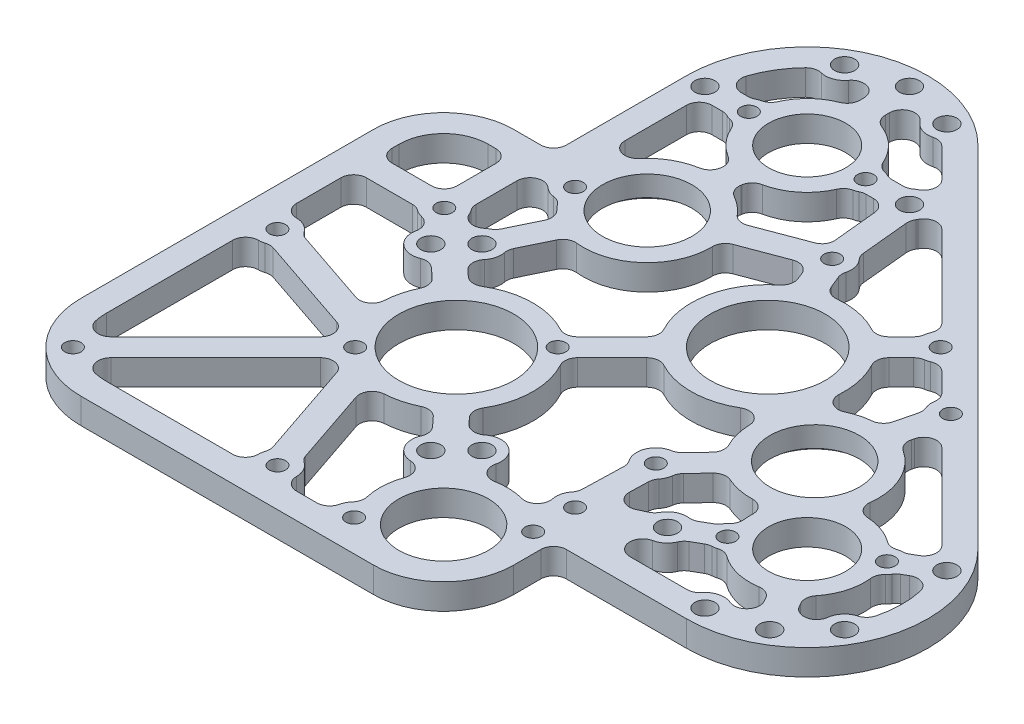
SolidWorks part; units mm, degrees
ref_plane "Front Plane" through (0, 0, 0) normal (0, 0, 1) x (1, 0, 0)
ref_plane "Top Plane" through (0, 0, 0) normal (0, 1, 0) x (1, 0, 0)
ref_plane "Right Plane" through (0, 0, 0) normal (1, 0, 0) x (0, 0, -1)
ref_plane "Plane1" through (0, 3.175, 0) normal (0, 1, 0) x (1, 0, 0)
sketch "Sketch1" plane through (0, 3.175, 0) normal (0, 1, 0) x (1, 0, 0)
  line L0 (-29.84, 86.9695) -> (-29.84, -29.84)
  line L1 (-29.84, -29.84) -> (86.9695, -29.84)
  line L2 (108.1827, 21.3732) -> (21.3732, 108.1827)
  arc A0 (86.9695, -29.84) -> (108.1827, 21.3732) centre (86.9695, 0.16) ccw
  arc A1 (21.3732, 108.1827) -> (-29.84, 86.9695) centre (0.16, 86.9695) ccw
extrude "Boss-Extrude1" add sketch "Sketch1" against normal blind 6.35
sketch "Sketch2" plane through (0, 0, 29.84) normal (0, 0, 1) x (1, 0, 0)
  line L0 (-29.84, 3.175) -> (53.975, 3.175)
  line L1 (53.975, 3.175) -> (53.975, -3.175)
  line L2 (53.975, -3.175) -> (-29.84, -3.175)
  line L3 (-29.84, -3.175) -> (-29.84, 3.175)
extrude "Boss-Extrude2" add sketch "Sketch2" along normal blind 27.31
sketch "Sketch3" plane through (-29.84, 0, 0) normal (-1, 0, 0) x (0, 0, 1)
  line L0 (-53.975, 3.175) -> (57.15, 3.175)
  line L1 (57.15, 3.175) -> (57.15, -3.175)
  line L2 (57.15, -3.175) -> (-53.975, -3.175)
  line L3 (-53.975, -3.175) -> (-53.975, 3.175)
extrude "Boss-Extrude3" add sketch "Sketch3" along normal blind 27.31
sketch "Sketch4" plane through (0, 3.175, 0) normal (0, 1, 0) x (-1, 0, 0)
  line L0 (-29.0653, -83.7455) -> (-30.4558, -69.5226)
  line L1 (-31.9225, -63.5944) -> (-34.5089, -57.2592)
  line L2 (-49.7059, -54.196) -> (-55.383, -59.8731)
  line L3 (-56.9235, -63.6521) -> (-34.9066, -85.6689)
  arc A0 (-34.9066, -85.6689) -> (-29.8209, -84.8421) centre (-32.6616, -83.4239) ccw
  arc A1 (-29.8209, -84.8421) -> (-29.0653, -83.7455) centre (-25.56, -86.9695) cw
  arc A2 (-30.4558, -69.5226) -> (-31.9225, -63.5944) centre (-27.6413, -65.6808) cw
  arc A3 (-34.5089, -57.2592) -> (-49.7059, -54.196) centre (-38.669, -38.669) cw
  arc A4 (-55.383, -59.8731) -> (-56.9235, -63.6521) centre (-60.1381, -60.1381) cw
extrude "Cut-Extrude1" cut sketch "Sketch4" against normal through all
sketch "Sketch5" plane through (0, 3.175, 0) normal (0, 1, 0) x (-1, 0, 0)
  line L0 (-96.6842, 10.3165) -> (-98.3364, 13.1781)
  line L1 (-105.4145, -7.1431) -> (-103.2213, -5.8768)
  arc A0 (-98.3364, 13.1781) -> (-104.2382, 11.9704) centre (-101.086, 11.5906) ccw
  arc A1 (-104.2382, 11.9704) -> (-109.2448, 7.7857) centre (-108.9665, 12.54) cw
  arc A2 (-109.2448, 7.7857) -> (-110.1084, -5.0499) centre (-86.9695, -0.16) ccw
  arc A3 (-110.1084, -5.0499) -> (-105.4145, -7.1431) centre (-107.002, -4.3934) ccw
  arc A4 (-103.2213, -5.8768) -> (-100.8296, -3.6281) centre (-99.5268, -7.41) cw
  arc A5 (-100.8296, -3.6281) -> (-96.6842, 10.3165) centre (-86.9695, -0.16) cw
extrude "Cut-Extrude2" cut sketch "Sketch5" against normal through all
sketch "Sketch6" plane through (0, 3.175, 0) normal (0, 1, 0) x (-1, 0, 0)
  line L0 (16.0612, -10.244) -> (22.0527, -15.6622)
  line L1 (35.0088, -25.2744) -> (50.8, -25.2744)
  line L2 (50.8, -25.2744) -> (50.8, -6.7248)
  line L3 (43.2449, -5.0448) -> (23.2061, 1.7351)
  arc A0 (23.2061, 1.7351) -> (19.0188, -1.0906) centre (22.1885, -1.2724) ccw
  arc A1 (19.0188, -1.0906) -> (16.0612, -10.244) centre (0, 0) cw
  arc A2 (22.0527, -15.6622) -> (30.0588, -20.0384) centre (25.4, -19.05) cw
  arc A3 (30.0588, -20.0384) -> (32.4824, -23.7981) centre (33.1647, -20.6973) ccw
  arc A4 (32.4824, -23.7981) -> (35.0088, -25.2744) centre (31.459, -28.4494) cw
  arc A5 (50.8, -6.7248) -> (43.2449, -5.0448) centre (47.625, -3.175) cw
extrude "Cut-Extrude3" cut sketch "Sketch6" against normal through all
sketch "Sketch7" plane through (0, 3.175, 0) normal (0, 1, 0) x (-1, 0, 0)
  line L0 (-24.2595, -96.3161) -> (-15.5435, -105.032)
  line L1 (-3.335, -104.204) -> (-3.335, -100.8997)
  line L2 (-17.093, -90.1445) -> (-22.0102, -90.1445)
  arc A0 (-22.0102, -90.1445) -> (-23.4326, -91.2304) centre (-25.56, -86.9695) cw
  arc A1 (-23.4326, -91.2304) -> (-24.2595, -96.3161) centre (-22.0144, -94.0711) ccw
  arc A2 (-15.5435, -105.032) -> (-9.05, -106.109) centre (-12.86, -108.9665) cw
  arc A3 (-9.05, -106.109) -> (-3.335, -104.204) centre (-6.51, -104.204) ccw
  arc A4 (-3.335, -100.8997) -> (-13.8973, -90.8961) centre (-0.16, -86.9695) cw
  arc A5 (-13.8973, -90.8961) -> (-17.093, -90.1445) centre (-14.66, -86.9695) cw
extrude "Cut-Extrude4" cut sketch "Sketch7" against normal through all
sketch "Sketch8" plane through (0, 3.175, 0) normal (0, 1, 0) x (-1, 0, 0)
  line L0 (-28.6299, -54.8591) -> (-25.8697, -61.6201)
  line L1 (-25.8697, -61.6201) -> (-9.958, -55.6236)
  line L2 (9.5999, -37.7167) -> (14.6498, -27.222)
  line L3 (18.1765, -20.7183) -> (11.8021, -14.9537)
  line L4 (-11.0369, -15.527) -> (-23.1419, -27.6321)
  arc A0 (-23.1419, -27.6321) -> (-28.6299, -54.8591) centre (-38.669, -38.669) cw
  arc A1 (-9.958, -55.6236) -> (9.5999, -37.7167) centre (5.7166, -53.1094) cw
  arc A2 (14.6498, -27.222) -> (18.1765, -20.7183) centre (19.05, -25.4) cw
  arc A3 (11.8021, -14.9537) -> (-11.0369, -15.527) centre (0, 0) cw
extrude "Cut-Extrude5" cut sketch "Sketch8" against normal through all
sketch "Sketch9" plane through (0, 3.175, 0) normal (0, 1, 0) x (-1, 0, 0)
  line L0 (-66.5703, 23.49) -> (-82.5401, 23.49)
  line L1 (-92.8371, 16.3531) -> (-91.185, 13.4915)
  line L2 (-73.8926, 11.0561) -> (-69.6341, 13.5148)
  arc A0 (-69.6341, 13.5148) -> (-65.9311, 17.205) centre (-64.9724, 12.54) cw
  arc A1 (-65.9311, 17.205) -> (-66.5703, 23.49) centre (-66.5703, 20.315) ccw
  arc A2 (-82.5401, 23.49) -> (-88.8403, 20.8604) centre (-86.9695, 25.24) cw
  arc A3 (-88.8403, 20.8604) -> (-92.8371, 16.3531) centre (-90.0875, 17.9406) ccw
  arc A4 (-91.185, 13.4915) -> (-77.0359, 10.1092) centre (-86.9695, -0.16) cw
  arc A5 (-77.0359, 10.1092) -> (-73.8926, 11.0561) centre (-74.4121, 7.09) cw
extrude "Cut-Extrude6" cut sketch "Sketch9" against normal through all
sketch "Sketch10" plane through (0, 3.175, 0) normal (0, 1, 0) x (-1, 0, 0)
  line L0 (-60.5829, -6.5299) -> (-54.5042, -0.1488)
  line L1 (-52.8316, 3.8684) -> (-52.6706, 9.6387)
  line L2 (-57.1631, 12.6155) -> (-60.4246, 11.1263)
  line L3 (-66.4591, 8.0155) -> (-70.7176, 5.5569)
  arc A0 (-73.4343, -4.7351) -> (-60.5829, -6.5299) centre (-69.0125, -19.9819) cw
  arc A1 (-54.5042, -0.1488) -> (-52.8316, 3.8684) centre (-49.7569, 0.2314) cw
  arc A2 (-52.6706, 9.6387) -> (-57.1631, 12.6155) centre (-55.8443, 9.7273) ccw
  arc A3 (-60.4246, 11.1263) -> (-66.4591, 8.0155) centre (-64.9724, 12.54) cw
  arc A4 (-70.7176, 5.5569) -> (-73.1093, 3.3081) centre (-74.4121, 7.09) cw
  arc A5 (-73.1093, 3.3081) -> (-73.4343, -4.7351) centre (-86.9695, -0.16) cw
extrude "Cut-Extrude7" cut sketch "Sketch10" against normal through all
sketch "Sketch11" plane through (0, 3.175, 0) normal (0, 1, 0) x (-1, 0, 0)
  line L0 (36.1273, 50.8) -> (0.3748, 50.8)
  line L1 (0.9702, 45.2801) -> (9.3987, 20.3689)
  line L2 (14.6513, 19.1414) -> (40.6599, 45.1501)
  arc A0 (0.3748, 50.8) -> (0.9702, 45.2801) centre (-3.175, 47.625) cw
  arc A1 (9.3987, 20.3689) -> (14.6513, 19.1414) centre (12.4062, 21.3865) ccw
  arc A2 (40.6599, 45.1501) -> (39.0466, 50.5067) centre (38.4149, 47.3951) ccw
  arc A3 (39.0466, 50.5067) -> (36.1273, 50.8) centre (36.1273, 36.1273) ccw
extrude "Cut-Extrude8" cut sketch "Sketch11" against normal through all
sketch "Sketch12" plane through (0, 3.175, 0) normal (0, 1, 0) x (-1, 0, 0)
  line L0 (28.284, -43.3699) -> (28.284, -31.9991)
  line L1 (20.3718, -29.9754) -> (15.3219, -40.4701)
  arc A0 (28.284, -31.9991) -> (27.0619, -30.2789) centre (31.459, -28.4494) cw
  arc A1 (27.0619, -30.2789) -> (22.0983, -29.0591) centre (24.1305, -31.4985) ccw
  arc A2 (22.0983, -29.0591) -> (20.3718, -29.9754) centre (19.05, -25.4) cw
  arc A3 (15.3219, -40.4701) -> (19.0537, -44.4991) centre (5.7166, -53.1094) cw
  arc A4 (19.0537, -44.4991) -> (22.9599, -45.7069) centre (19.7361, -49.2125) cw
  arc A5 (22.9599, -45.7069) -> (28.284, -43.3699) centre (25.109, -43.3699) ccw
extrude "Cut-Extrude9" cut sketch "Sketch12" against normal through all
sketch "Sketch13" plane through (0, 3.175, 0) normal (0, 1, 0) x (-1, 0, 0)
  line L0 (-69.6829, -35.8427) -> (-71.8085, -44.3955)
  line L1 (-71.4484, -49.1272) -> (-63.6521, -56.9235)
  line L2 (-59.8731, -55.383) -> (-54.196, -49.7059)
  arc A0 (-54.196, -49.7059) -> (-57.6769, -37.4031) centre (-38.669, -38.669) cw
  arc A1 (-57.6769, -37.4031) -> (-62.2061, -34.3237) centre (-60.8449, -37.1921) ccw
  arc A2 (-62.2061, -34.3237) -> (-69.6829, -35.8427) centre (-69.0125, -19.9819) cw
  arc A3 (-71.8085, -44.3955) -> (-71.4484, -49.1272) centre (-75.7459, -47.0747) cw
  arc A4 (-63.6521, -56.9235) -> (-59.8731, -55.383) centre (-60.1381, -60.1381) cw
extrude "Cut-Extrude10" cut sketch "Sketch13" against normal through all
sketch "Sketch14" plane through (0, 3.175, 0) normal (0, 1, 0) x (-1, 0, 0)
  line L0 (-46.1378, 16.0992) -> (-46.4841, 3.6912)
  line L1 (-49.9065, -4.5287) -> (-55.9852, -10.9098)
  line L2 (-27.6321, -23.1419) -> (-15.527, -11.0369)
  line L3 (-15.0548, 11.6729) -> (-20.7797, 17.895)
  arc A0 (-44.546, 20.6875) -> (-46.1378, 16.0992) centre (-49.2125, 19.7361) cw
  arc A1 (-46.4841, 3.6912) -> (-49.9065, -4.5287) centre (-49.7569, 0.2314) cw
  arc A2 (-55.9852, -10.9098) -> (-53.142, -19.6057) centre (-69.0125, -19.9819) cw
  arc A3 (-53.142, -19.6057) -> (-48.3538, -22.2645) centre (-49.9679, -19.5304) ccw
  arc A4 (-48.3538, -22.2645) -> (-27.6321, -23.1419) centre (-38.669, -38.669) cw
  arc A5 (-15.527, -11.0369) -> (-15.0548, 11.6729) centre (0, 0) cw
  arc A6 (-20.7797, 17.895) -> (-30.0155, 20.2243) centre (-25.4, 19.05) cw
  arc A7 (-30.0155, 20.2243) -> (-33.6709, 24.129) centre (-33.0924, 21.0071) ccw
  arc A8 (-33.6709, 24.129) -> (-40.623, 24.3911) centre (-36.5633, 39.7383) cw
  arc A9 (-40.623, 24.3911) -> (-44.546, 20.6875) centre (-41.435, 21.3217) ccw
extrude "Cut-Extrude11" cut sketch "Sketch14" against normal through all
sketch "Sketch15" plane through (0, 3.175, 0) normal (0, 1, 0) x (-1, 0, 0)
  line L0 (-0.9062, -72.7015) -> (-0.0714, -67.8917)
  line L1 (-7.7187, -61.5657) -> (-22.0651, -66.9723)
  line L2 (-24.018, -70.1117) -> (-22.6803, -83.7945)
  line L3 (-22.6803, -83.7945) -> (-17.093, -83.7945)
  arc A0 (-0.0714, -67.8917) -> (-7.7187, -61.5657) centre (5.7166, -53.1094) cw
  arc A1 (-22.0651, -66.9723) -> (-23.5968, -68.1966) centre (-20.9454, -69.9433) ccw
  arc A2 (-23.5968, -68.1966) -> (-24.018, -70.1117) centre (-20.858, -69.8028) ccw
  arc A3 (-17.093, -83.7945) -> (-13.8973, -83.0428) centre (-14.66, -86.9695) cw
  arc A4 (-13.8973, -83.0428) -> (-0.9062, -72.7015) centre (-0.16, -86.9695) cw
extrude "Cut-Extrude12" cut sketch "Sketch15" against normal through all
sketch "Sketch16" plane through (0, 3.175, 0) normal (0, 1, 0) x (-1, 0, 0)
  line L0 (23.49, -83.7945) -> (23.49, -65.3482)
  line L1 (6.1851, -68.9775) -> (5.3503, -73.7873)
  line L2 (16.773, -83.7945) -> (23.49, -83.7945)
  arc A0 (23.49, -65.3482) -> (17.882, -63.3084) centre (20.315, -65.3482) ccw
  arc A1 (17.882, -63.3084) -> (6.1851, -68.9775) centre (5.7166, -53.1094) cw
  arc A2 (5.3503, -73.7873) -> (13.5774, -83.0428) centre (-0.16, -86.9695) cw
  arc A3 (13.5774, -83.0428) -> (16.773, -83.7945) centre (14.34, -86.9695) cw
extrude "Cut-Extrude13" cut sketch "Sketch16" against normal through all
sketch "Sketch17" plane through (0, 3.175, 0) normal (0, 1, 0) x (-1, 0, 0)
  line L0 (50.8, -31.6244) -> (34.634, -31.6244)
  line L1 (34.634, -31.6244) -> (34.634, -47.625)
  line L2 (34.634, -47.625) -> (50.8, -47.625)
  line L3 (50.8, -47.625) -> (50.8, -31.6244)
extrude "Cut-Extrude14" cut sketch "Sketch17" against normal through all
sketch "Sketch18" plane through (0, 3.175, 0) normal (0, 1, 0) x (-1, 0, 0)
  line L0 (-15.8286, 21.8923) -> (-10.3818, 15.9725)
  line L1 (1.7351, 23.2061) -> (-5.0448, 43.2449)
  line L2 (-6.7248, 50.8) -> (-19.3839, 50.8)
  arc A0 (-18.7949, 30.1557) -> (-15.8286, 21.8923) centre (-19.05, 25.4) cw
  arc A1 (-10.3818, 15.9725) -> (-1.0906, 19.0188) centre (0, 0) cw
  arc A2 (-1.0906, 19.0188) -> (1.7351, 23.2061) centre (-1.2724, 22.1885) ccw
  arc A3 (-5.0448, 43.2449) -> (-6.7248, 50.8) centre (-3.175, 47.625) cw
  arc A4 (-19.3839, 50.8) -> (-21.6381, 45.1471) centre (-23.914, 49.3306) cw
  arc A5 (-21.6381, 45.1471) -> (-21.6146, 34.3948) centre (-36.5633, 39.7383) cw
  arc A6 (-21.6146, 34.3948) -> (-18.7949, 30.1557) centre (-18.6248, 33.3261) ccw
extrude "Cut-Extrude15" cut sketch "Sketch18" against normal through all
sketch "Sketch19" plane through (0, 3.175, 0) normal (0, 1, 0) x (-1, 0, 0)
  line L0 (-102.9234, -17.6522) -> (-81.891, -38.6846)
  line L1 (-76.5647, -37.2053) -> (-75.8454, -34.3112)
  line L2 (-100.0463, -11.3761) -> (-102.2658, -12.6575)
  arc A0 (-102.2658, -12.6575) -> (-102.9234, -17.6522) centre (-100.6783, -15.4071) ccw
  arc A1 (-81.891, -38.6846) -> (-76.5647, -37.2053) centre (-79.6459, -36.4395) ccw
  arc A2 (-75.8454, -34.3112) -> (-83.7497, -14.0799) centre (-69.0125, -19.9819) cw
  arc A3 (-83.7497, -14.0799) -> (-96.903, -10.4292) centre (-86.9695, -0.16) cw
  arc A4 (-96.903, -10.4292) -> (-100.0463, -11.3761) centre (-99.5268, -7.41) cw
extrude "Cut-Extrude16" cut sketch "Sketch19" against normal through all
sketch "Sketch20" plane through (0, 3.175, 0) normal (0, 1, 0) x (-1, 0, 0)
  line L0 (3.015, -100.8997) -> (3.015, -104.204)
  line L1 (19.3055, -90.1445) -> (16.773, -90.1445)
  arc A0 (3.015, -104.204) -> (8.73, -106.109) centre (6.19, -104.204) ccw
  arc A1 (8.73, -106.109) -> (15.1582, -104.9882) centre (12.54, -108.9665) cw
  arc A2 (15.1582, -104.9882) -> (22.3239, -94.3041) centre (-0.16, -86.9695) ccw
  arc A3 (22.3239, -94.3041) -> (19.3055, -90.1445) centre (19.3055, -93.3195) ccw
  arc A4 (16.773, -90.1445) -> (13.5774, -90.8961) centre (14.34, -86.9695) cw
  arc A5 (13.5774, -90.8961) -> (3.015, -100.8997) centre (-0.16, -86.9695) cw
extrude "Cut-Extrude17" cut sketch "Sketch20" against normal through all
sketch "Sketch21" plane through (0, -3.175, 0) normal (0, -1, 0) x (1, 0, 0)
  line L0 (-45.2801, 0.9702) -> (-20.3689, 9.3987)
  line L1 (-19.1414, 14.6513) -> (-45.1501, 40.6599)
  line L2 (-50.8, 36.1273) -> (-50.8, 0.3748)
  arc A0 (-20.3689, 9.3987) -> (-19.1414, 14.6513) centre (-21.3865, 12.4062) ccw
  arc A1 (-45.1501, 40.6599) -> (-50.5067, 39.0466) centre (-47.3951, 38.4149) ccw
  arc A2 (-50.5067, 39.0466) -> (-50.8, 36.1273) centre (-36.1273, 36.1273) ccw
  arc A3 (-50.8, 0.3748) -> (-45.2801, 0.9702) centre (-47.625, -3.175) cw
extrude "Cut-Extrude18" cut sketch "Sketch21" against normal through all
sketch "Sketch22" plane through (0, -3.175, 0) normal (0, -1, 0) x (1, 0, 0)
  arc A0 (-19.0603, -46.5015) -> (-20.5562, -51.8834) centre (-19.7361, -49.2125) ccw
  arc A1 (-20.5562, -51.8834) -> (-18.3339, -54.5567) centre (-21.4882, -54.9186) cw
  arc A2 (-18.3339, -54.5567) -> (-15.7771, -45.3585) centre (-5.7166, -53.1094) ccw
  arc A3 (-15.7771, -45.3585) -> (-19.0603, -46.5015) centre (-18.2922, -43.4208) cw
extrude "Cut-Extrude19" cut sketch "Sketch22" against normal blind 1.27
hole_wizard "7/8 (0.875) Diameter Hole1" positions "Sketch24" profile "Sketch23" hole size "7/8" standard "ANSI Inch"
sketch "Sketch24" plane through (0, -1.905, 0) normal (0, -1, 0) x (-1, 0, 0)
  point P0 (5.7166, 53.1094)
sketch "Sketch23" plane through (-5.7166, -1.905, -53.1094) normal (1, 0, 0) x (0, 0, -1)
  line L0 (0, 0) -> (0, 5.08)
  line L1 (0, 5.08) -> (11.1125, 5.08)
  line L2 (11.1125, 5.08) -> (11.1125, 0)
  line L5 (11.1125, 0) -> (0, 0)
  line L11 (0, -6.35) -> (0, 107.95) construction
  dimension "Thru Hole Dia." = 22.225
  dimension "Thru Hole Depth" = 5.08
hole_wizard "Hole1" positions "Sketch26" profile "Sketch25" legacy
sketch "Sketch26" plane through (0, -3.175, 0) normal (0, -1, 0) x (-1, 0, 0)
  point P0 (-86.9695, 0.16)
  point P1 (-0.16, 86.9695)
sketch "Sketch25" plane through (86.9695, -3.175, -0.16) normal (1, 0, 0) x (0, 0, -1)
  line L0 (0, 0) -> (0, 6.35)
  line L1 (0, 6.35) -> (9.5885, 6.35)
  line L2 (9.5885, 6.35) -> (9.5885, 0)
  line L3 (9.5885, 0) -> (0, 0)
  line L4 (0, 110) -> (0, -10) construction
  dimension "Diameter" = 19.177
  dimension "Depth" = 6.35
hole_wizard "#9 (0.196) Diameter Hole1" positions "Sketch28" profile "Sketch27" hole size "#9" standard "ANSI Inch"
sketch "Sketch28" plane through (0, -3.175, 0) normal (0, -1, 0) x (-1, 0, 0)
  point P0 (-25.4, -19.05)
  point P1 (-19.05, -25.4)
  point P2 (19.05, 25.4)
  point P3 (25.4, 19.05)
  point P4 (-0.16, 112.3695)
  point P5 (12.54, 108.9665)
  point P6 (-86.9695, -25.24)
  point P7 (-99.6695, -21.8371)
  point P8 (-25.56, 86.9695)
  point P9 (-108.9665, -12.54)
  point P10 (-108.9665, 12.86)
  point P11 (-64.9724, -12.54)
  point P12 (-12.86, 108.9665)
  point P13 (25.24, 86.9695)
sketch "Sketch27" plane through (25.4, -3.175, 19.05) normal (1, 0, 0) x (0, 0, -1)
  line L0 (0, 0) -> (0, 6.35)
  line L1 (0, 6.35) -> (2.4892, 6.35)
  line L2 (2.4892, 6.35) -> (2.4892, 0)
  line L5 (2.4892, 0) -> (0, 0)
  line L11 (0, -6.35) -> (0, 107.95) construction
  dimension "Thru Hole Dia." = 4.9784
  dimension "Thru Hole Depth" = 6.35
hole_wizard "#21 (0.159) Diameter Hole1" positions "Sketch30" profile "Sketch29" hole size "#21" standard "ANSI Inch"
sketch "Sketch30" plane through (0, -1.905, 0) normal (0, -1, 0) x (-1, 0, 0)
  point P0 (19.7361, 49.2125)
sketch "Sketch29" plane through (-19.7361, -1.905, -49.2125) normal (1, 0, 0) x (0, 0, -1)
  line L0 (0, 0) -> (0, 5.08)
  line L1 (0, 5.08) -> (2.0193, 5.08)
  line L2 (2.0193, 5.08) -> (2.0193, 0)
  line L5 (2.0193, 0) -> (0, 0)
  line L11 (0, -6.35) -> (0, 107.95) construction
  dimension "Thru Hole Dia." = 4.0386
  dimension "Thru Hole Depth" = 5.08
hole_wizard "#21 (0.159) Diameter Hole2" positions "Sketch32" profile "Sketch31" hole size "#21" standard "ANSI Inch"
sketch "Sketch32" plane through (0, -3.175, 0) normal (0, -1, 0) x (-1, 0, 0)
  point P0 (-49.2125, -30.146)
  point P1 (-23.914, -49.3306)
  point P2 (-49.2125, -19.7361)
  point P3 (47.625, -47.625)
  point P4 (-99.5268, 7.41)
  point P5 (14.34, 86.9695)
  point P6 (-14.66, 86.9695)
  point P7 (-74.4121, -7.09)
  point P8 (47.625, 3.175)
  point P9 (-3.175, -47.625)
  point P10 (-60.1381, 60.1381)
  point P11 (-27.6413, 65.6808)
  point P12 (-49.7569, -0.2314)
  point P13 (-75.7459, 47.0747)
  point P14 (31.459, 28.4494)
sketch "Sketch31" plane through (49.2125, -3.175, 30.146) normal (1, 0, 0) x (0, 0, -1)
  line L0 (0, 0) -> (0, 6.35)
  line L1 (0, 6.35) -> (2.0193, 6.35)
  line L2 (2.0193, 6.35) -> (2.0193, 0)
  line L5 (2.0193, 0) -> (0, 0)
  line L11 (0, -6.35) -> (0, 107.95) construction
  dimension "Thru Hole Dia." = 4.0386
  dimension "Thru Hole Depth" = 6.35
hole_wizard "7/8 (0.875) Diameter Hole2" positions "Sketch34" profile "Sketch33" hole size "7/8" standard "ANSI Inch"
sketch "Sketch34" plane through (0, -3.175, 0) normal (0, -1, 0) x (-1, 0, 0)
  point P0 (-36.5633, -39.7383)
sketch "Sketch33" plane through (36.5633, -3.175, 39.7383) normal (1, 0, 0) x (0, 0, -1)
  line L0 (0, 0) -> (0, 6.35)
  line L1 (0, 6.35) -> (11.1125, 6.35)
  line L2 (11.1125, 6.35) -> (11.1125, 0)
  line L5 (11.1125, 0) -> (0, 0)
  line L11 (0, -6.35) -> (0, 107.95) construction
  dimension "Thru Hole Dia." = 22.225
  dimension "Thru Hole Depth" = 6.35
hole_wizard "Hole2" positions "Sketch36" profile "Sketch35" legacy
sketch "Sketch36" plane through (0, 3.175, 0) normal (0, 1, 0) x (1, 0, 0)
  point P0 (38.669, 38.669)
  point P1 (0, 0)
sketch "Sketch35" plane through (38.669, 3.175, -38.669) normal (1, 0, 0) x (0, 0, 1)
  line L0 (0, 0) -> (0, 6.35)
  line L1 (0, 6.35) -> (14.2875, 6.35)
  line L2 (14.2875, 6.35) -> (14.2875, 0)
  line L3 (14.2875, 0) -> (0, 0)
  line L4 (0, 110) -> (0, -10) construction
  dimension "Diameter" = 28.575
  dimension "Depth" = 6.35
hole_wizard "1-12 Tapped Hole1" positions "Sketch38" profile "Sketch37" tap size "1-12" standard "ANSI Inch"
sketch "Sketch38" plane through (0, -3.175, 0) normal (0, -1, 0) x (-1, 0, 0)
  point P0 (-69.0125, 19.9819)
sketch "Sketch37" plane through (69.0125, -3.175, -19.9819) normal (1, 0, 0) x (0, 0, -1)
  line L0 (0, 0) -> (0, 6.35)
  line L1 (0, 6.35) -> (11.1125, 6.35)
  line L3 (11.1125, 6.35) -> (11.1125, 1.27)
  line L4 (11.1125, 1.27) -> (12.7, 1.27)
  line L5 (12.7, 1.27) -> (12.7, 0)
  line L7 (12.7, 0) -> (0, 0)
  line L11 (0, -6.35) -> (0, 107.95) construction
  dimension "Thru Tap Drill Dia." = 22.225
  dimension "Thru Tap Drill Depth" = 6.35
  dimension "Thread Major Dia." = 25.4
  dimension "Thread Depth" = 1.27
fillet "Fillet1" radius 3.175 96 edges at (59.8731, 0, -55.383) (-43.2449, 0, -5.0448) (-6.1851, 0, -68.9775) (60.5829, 0, -6.5299) (-5.3503, 0, -73.7873) (-34.634, 0, -31.6244) (46.1378, 0, 16.0992) (77.0359, 0, 10.1092) (15.8286, 0, 21.8923) (3.335, 0, -100.8997) (19.3839, 0, 50.8) (69.6829, 0, -35.8427) (21.6381, 0, 45.1471) (-35.0088, 0, -25.2744) (0.9062, 0, -72.7015) (-50.8, 0, 0.3748) (0.0714, 0, -67.8917) (-19.0537, 0, -44.4991) (23.1419, 0, -27.6321) (73.4343, 0, -4.7351) (-9.5999, 0, -37.7167) (91.185, 0, 13.4915) (-14.6498, 0, -27.222) (49.9065, 0, -4.5287) (27.6321, 0, -23.1419) (75.8454, 0, -34.3112) (15.527, 0, -11.0369) (55.383, 0, -59.8731) (15.0548, 0, 11.6729) (-16.0612, 0, -10.244) (83.7497, 0, -14.0799) (-28.284, 0, -31.9991) (-23.49, 0, -83.7945) (-0.9702, 0, 45.2801) (25.8697, 0, -61.6201) (6.7248, 0, 50.8) (29.0653, 0, -83.7455) (60.4246, 0, 11.1263) (30.4558, 0, -69.5226) (10.3818, 0, 15.9725) (31.9225, 0, -63.5944) (34.5089, 0, -57.2592) (28.6299, 0, -54.8591) (11.0369, 0, -15.527) (96.6842, 0, 10.3165) (-3.015, 0, -100.8997) (22.6803, 0, -83.7945) (71.8085, 0, -44.3955) (71.4484, 0, -49.1272) (55.9852, 0, -10.9098) (54.196, 0, -49.7059) (54.5042, 0, -0.1488) (103.2213, 0, -5.8768) (9.958, 0, -55.6236) (100.8296, 0, -3.6281) (63.6521, 0, -56.9235) (73.8926, 0, 11.0561) (56.9235, 0, -63.6521) (82.5401, 0, 23.49) (-34.634, 0, -47.625) (109.2448, 0, 7.7857) (-22.0527, 0, -15.6622) (-13.5774, 0, -83.0428) (-50.8, 0, -25.2744) (-16.773, 0, -83.7945) (-18.1765, 0, -20.7183) (17.093, 0, -83.7945) (-50.8, 0, -31.6244) (13.8973, 0, -83.0428) (-45.2801, 0, 0.9702) (70.7176, 0, 5.5569) (-0.3748, 0, 50.8) (73.1093, 0, 3.3081) (-50.8, 0, -6.7248) (96.903, 0, -10.4292) (52.8316, 0, 3.8684) (100.0463, 0, -11.3761) (-20.3718, 0, -29.9754) (-15.3219, 0, -40.4701) (53.975, 0, 29.84) (13.8973, 0, -90.8961) (-29.84, 0, -53.975) (5.0448, 0, 43.2449) (22.0102, 0, -90.1445) (-11.8021, 0, -14.9537) (17.093, 0, -90.1445) (7.7187, 0, -61.5657) (15.5435, 0, -105.032) (49.7059, 0, -54.196) (-15.1582, 0, -104.9882) (66.4591, 0, 8.0155) (-16.773, 0, -90.1445) (20.7797, 0, 17.895) (-13.5774, 0, -90.8961) (69.6341, 0, 13.5148) (46.4841, 0, 3.6912)
fillet "Fillet2" radius 11.0617 1 edges at (-50.8, 0, -47.625)
fillet "Fillet3" radius 17.4117 2 edges at (-57.15, 0, -53.975) (53.975, 0, 57.15)
fillet "Fillet4" radius 21.0227 1 edges at (-57.15, 0, 57.15)
sketch "Sketch39" plane through (0, 3.175, 0) normal (0, 1, 0) x (1, 0, 0)
  line L5 (-12.5724, -12.5724) -> (12.5724, 12.5724) construction
  line L6 (25.8537, 21.3636) -> (17.3054, 12.8153) construction
  circle A4 centre (0, 0) radius 17.78 construction
  point P0 (12.5724, 12.5724)
  point P4 (-12.5724, -12.5724)
  dimension "D3" = 35.56
  dimension "D1" = 3.175
hole_wizard "#21 (0.159) Diameter Hole3" positions "Sketch40" profile "Sketch41" hole size "#21" standard "ANSI Inch" end condition through all
sketch "Sketch40" plane through (0, 3.175, 0) normal (0, 1, 0) x (1, 0, 0)
  point P0 (12.5724, 12.5724)
  point P3 (-12.5724, -12.5724)
sketch "Sketch41" plane through (12.5724, 3.175, -12.5724) normal (1, 0, 0) x (0, 0, 1)
  line L0 (0, 0) -> (0, 6.35)
  line L1 (0, 6.35) -> (2.0193, 6.35)
  line L2 (2.0193, 6.35) -> (2.0193, 0)
  line L5 (2.0193, 0) -> (0, 0)
  line L11 (0, -6.35) -> (0, 107.95) construction
  dimension "Thru Hole Dia." = 4.0386
  dimension "Thru Hole Depth" = 6.35
